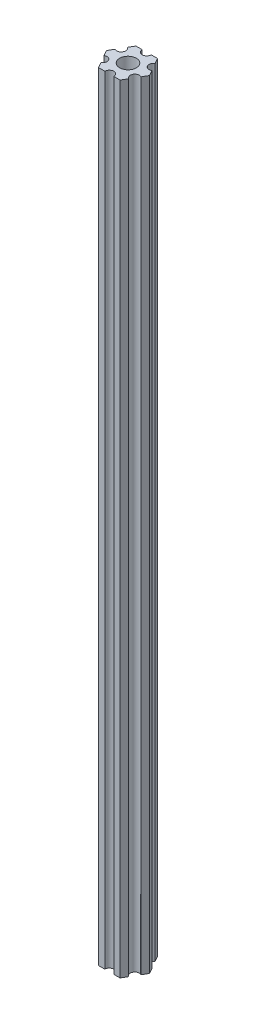
SolidWorks part; units mm, degrees
material "Churro - 6005A-T61"
ref_plane "Plano frontal" through (0, 0, 0) normal (0, 0, 1) x (1, 0, 0)
ref_plane "Plano superior" through (0, 0, 0) normal (0, 1, 0) x (1, 0, 0)
ref_plane "Plano direito" through (0, 0, 0) normal (1, 0, 0) x (0, 0, -1)
ref_plane "Plano1" through (0, 85, 0) normal (0, 1, 0) x (1, 0, 0)
sketch "Esboço1" plane through (0, 85, 0) normal (0, 1, 0) x (1, 0, 0)
  line L0 (6.1627, -1.826) -> (7.2169, 0)
  line L1 (7.2169, 0) -> (6.1627, 1.826)
  line L2 (4.6627, 4.424) -> (3.6084, 6.25)
  line L3 (3.6084, 6.25) -> (1.5, 6.25)
  line L4 (-1.5, 6.25) -> (-3.6084, 6.25)
  line L5 (-3.6084, 6.25) -> (-4.6627, 4.424)
  line L6 (-6.1627, 1.826) -> (-7.2169, 0)
  line L7 (-7.2169, 0) -> (-6.1627, -1.826)
  line L8 (-4.6627, -4.424) -> (-3.6084, -6.25)
  line L9 (-3.6084, -6.25) -> (-1.5, -6.25)
  line L10 (1.5, -6.25) -> (3.6084, -6.25)
  line L11 (3.6084, -6.25) -> (4.6627, -4.424)
  arc A0 (6.1627, 1.826) -> (4.6627, 4.424) centre (5.4127, 3.125) cw
  arc A1 (1.5, 6.25) -> (-1.5, 6.25) centre (0, 6.25) cw
  arc A2 (-4.6627, 4.424) -> (-6.1627, 1.826) centre (-5.4127, 3.125) cw
  arc A3 (-6.1627, -1.826) -> (-4.6627, -4.424) centre (-5.4127, -3.125) cw
  arc A4 (-1.5, -6.25) -> (1.5, -6.25) centre (0, -6.25) cw
  arc A5 (4.6627, -4.424) -> (6.1627, -1.826) centre (5.4127, -3.125) cw
  circle A6 centre (0, 0) radius 2.79
extrude "Ressalto-extrusão1" add sketch "Esboço1" against normal blind 260
